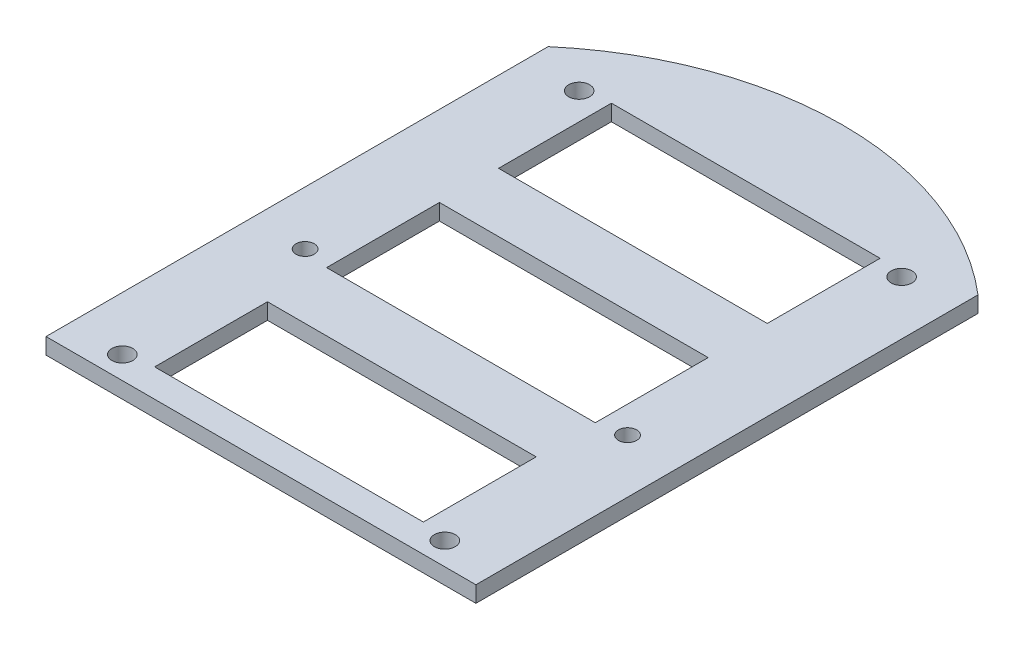
SolidWorks part; units mm, degrees
material "PF"
ref_plane "Plan de face" through (0, 0, 0) normal (0, 0, 1) x (1, 0, 0)
ref_plane "Plan de dessus" through (0, 0, 0) normal (0, 1, 0) x (1, 0, 0)
ref_plane "Plan de droite" through (0, 0, 0) normal (1, 0, 0) x (0, 0, -1)
sketch "Esquisse1" plane through (0, 0, 0) normal (0, 1, 0) x (1, 0, 0)
  circle A0 centre (0, 0) radius 61.5
  dimension "D1" = 123
extrude "Boss.-Extru.1" add sketch "Esquisse1" along normal blind 3
sketch "Esquisse3" plane through (0, 3, 0) normal (0, 1, 0) x (1, 0, 0)
  line L0 (0, 0) -> (0, 63.5107) construction
  line L1 (-40, 47.3401) -> (-40, -67.2604)
  line L2 (-40, -67.2604) -> (-70.4664, -67.2604)
  line L3 (-70.4664, -67.2604) -> (-70.4664, 47.3401)
  line L4 (-70.4664, 47.3401) -> (-40, 47.3401)
  line L5 (40, -67.2604) -> (70.4664, -67.2604)
  line L6 (70.4664, -67.2604) -> (70.4664, 47.3401)
  line L7 (70.4664, 47.3401) -> (40, 47.3401)
  line L8 (40, 47.3401) -> (40, -67.2604)
  dimension "D1" = 40
extrude "Enlèv. mat.-Extru.1" cut sketch "Esquisse3" against normal through all
sketch "Esquisse4" plane through (0, 3, 0) normal (0, 1, 0) x (1, 0, 0)
  line L0 (-40, -8.5) -> (40, -8.5) construction
  line L1 (0, 61.5) -> (0, -61.5) construction
  arc A0 (40, 46.7146) -> (-40, 46.7146) centre (0, 0) ccw construction
  arc A1 (-40, -46.7146) -> (40, -46.7146) centre (0, 0) ccw construction
  dimension "D1" = 70
sketch "Esquisse10" plane through (0, 3, 0) normal (0, 1, 0) x (1, 0, 0)
  line L1 (30, -42.5) -> (-30, -42.5)
  line L2 (30, -42.5) -> (30, 42.5)
  line L3 (30, 42.5) -> (-30, 42.5)
  line L4 (-30, -42.5) -> (-30, 42.5)
  line L5 (30, -42.5) -> (-30, 42.5) construction
  line L6 (30, 42.5) -> (-30, -42.5) construction
  point P0 (0, 0)
  dimension "D1" = 85
  dimension "D2" = 60
hole_wizard "Dégagement M31" positions "Esquisse8" profile "Esquisse7" hole size "M3" standard "Iso" end condition through all
sketch "Esquisse8" plane through (0, 3, 0) normal (0, 1, 0) x (1, 0, 0)
  line L0 (-40, -8.5) -> (40, -8.5) construction
  line L1 (0, 61.5) -> (0, -61.5) construction
  point P0 (-30, -8.5)
  dimension "D1" = 30
sketch "Esquisse7" plane through (-30, 3, 8.5) normal (1, 0, 0) x (0, 0, 1)
  line L0 (0, 0) -> (0, 3)
  line L1 (0, 3) -> (1.7, 3)
  line L2 (1.7, 3) -> (1.7, 0)
  line L5 (1.7, 0) -> (0, 0)
  line L11 (0, -6.35) -> (0, 107.95) construction
  dimension "Diamètre du perçage jusqu'au prochain" = 3.4
  dimension "Profondeur du perçage jusqu'au prochain" = 3
ref_plane "Plan1" through (0, 0, 0) normal (-1, 0, 0) x (0, 0, 1)
mirror "Symétrie1" about plane through (0, 0, 0) normal (-1, 0, 0) of "Dégagement M31"
hole_wizard "Dégagement M3.51" positions "Esquisse12" profile "Esquisse13" hole size "M3.5" standard "Iso" end condition through all
sketch "Esquisse12" plane through (0, 3, 0) normal (0, 1, 0) x (1, 0, 0)
  point P0 (-30, 42.5)
  point P3 (30, 42.5)
  point P6 (30, -42.5)
  point P9 (-30, -42.5)
sketch "Esquisse13" plane through (-30, 3, -42.5) normal (1, 0, 0) x (0, 0, 1)
  line L0 (0, 0) -> (0, 3)
  line L1 (0, 3) -> (1.95, 3)
  line L2 (1.95, 3) -> (1.95, 0)
  line L5 (1.95, 0) -> (0, 0)
  line L11 (0, -6.35) -> (0, 107.95) construction
  dimension "Diamètre du perçage jusqu'au prochain" = 3.9
  dimension "Profondeur du perçage jusqu'au prochain" = 3
sketch "Esquisse15" plane through (0, 3, 0) normal (0, 1, 0) x (1, 0, 0)
  line L0 (0, 61.5) -> (0, -61.5) construction
  line L1 (25, 22.5) -> (-25, 22.5)
  line L2 (25, 22.5) -> (25, 43.5)
  line L3 (25, 43.5) -> (-25, 43.5)
  line L4 (-25, 22.5) -> (-25, 43.5)
  line L5 (25, 22.5) -> (-25, 43.5) construction
  line L6 (25, 43.5) -> (-25, 22.5) construction
  line L7 (-40, -46.7146) -> (40, -46.7146)
  line L8 (25, -41.5) -> (-25, -41.5)
  line L9 (25, -41.5) -> (25, -20.5)
  line L10 (25, -20.5) -> (-25, -20.5)
  line L11 (-25, -41.5) -> (-25, -20.5)
  line L12 (25, -41.5) -> (-25, -20.5) construction
  line L13 (25, -20.5) -> (-25, -41.5) construction
  line L14 (25, -9.5) -> (-25, -9.5)
  line L15 (25, -9.5) -> (25, 11.5)
  line L16 (25, 11.5) -> (-25, 11.5)
  line L17 (-25, -9.5) -> (-25, 11.5)
  line L18 (25, -9.5) -> (-25, 11.5) construction
  line L19 (25, 11.5) -> (-25, -9.5) construction
  line L20 (40, -46.7146) -> (40, -63.3773)
  line L21 (40, -63.3773) -> (-40, -63.3773)
  line L22 (-40, -63.3773) -> (-40, -46.7146)
  point P0 (0, 33)
  point P7 (0, -31)
  point P12 (0, 1)
  dimension "D1" = 21
  dimension "D2" = 50
  dimension "D3" = 18
  dimension "D4" = 11
  dimension "D5" = 11
extrude "Enlèv. mat.-Extru.2" cut sketch "Esquisse15" against normal through all
